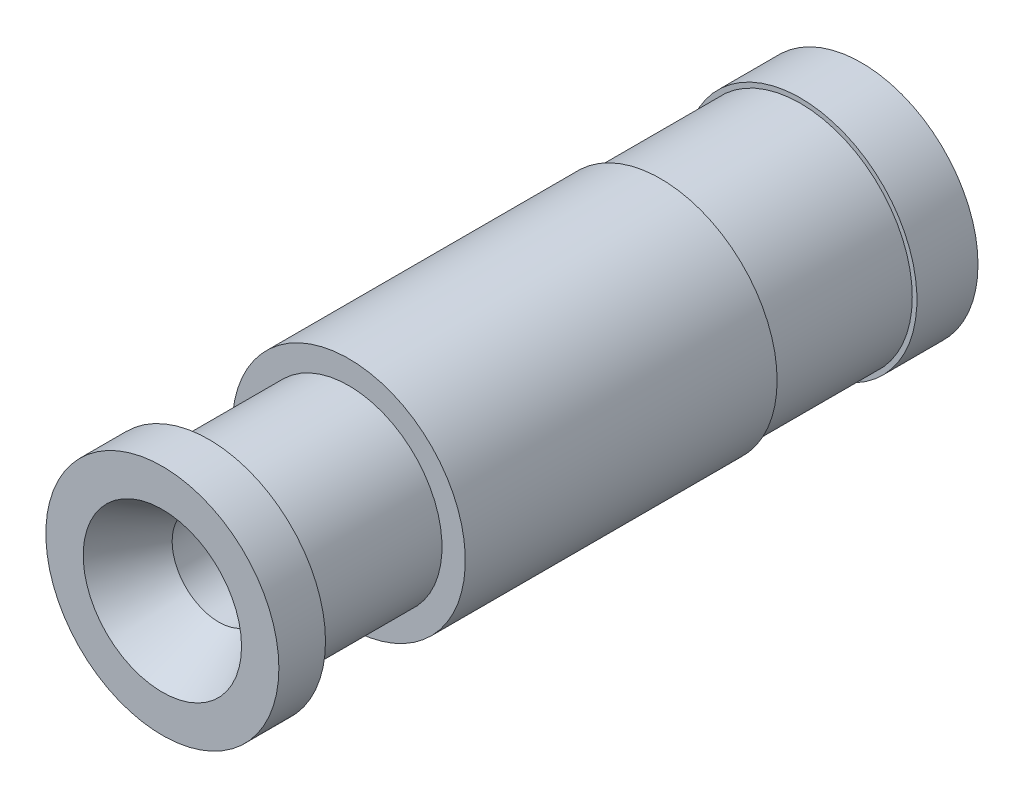
SolidWorks part; units mm, degrees
material "Brass"
ref_plane "Front Plane" through (0, 0, 0) normal (0, 0, 1) x (1, 0, 0)
ref_plane "Top Plane" through (0, 0, 0) normal (0, 1, 0) x (1, 0, 0)
ref_plane "Right Plane" through (0, 0, 0) normal (1, 0, 0) x (0, 0, -1)
sketch "Sketch1" plane through (0, 0, 0) normal (0, 0, 1) x (1, 0, 0)
  circle A0 centre (0, 0) radius 2.5
  dimension "D1" = 5
extrude "Boss-Extrude1" add sketch "Sketch1" along normal blind 15
sketch "Sketch2" plane through (0, 0, 0) normal (0, 0, -1) x (-1, 0, 0)
  circle A0 centre (0, 0) radius 1
  dimension "D1" = 2
extrude "Cut-Extrude1" cut sketch "Sketch2" against normal through all
hole_wizard "Tap Drill for M4x0.7 Tap1" positions "Sketch4" profile "Sketch3" hole size "M4x0.7" standard "ANSI Metric"
sketch "Sketch4" plane through (0, 0, 0) normal (0, 0, -1) x (-1, 0, 0)
  point P0 (0, 0)
cosmetic thread "Cosmetic Thread1" parameters "D1"=8, "D2"=4
sketch "Sketch3" plane through (0, 0, 0) normal (1, 0, 0) x (0, 1, 0)
  line L0 (0, 0) -> (0, 9.9914)
  line L1 (0, 9.9914) -> (1.65, 9)
  line L2 (1.65, 9) -> (1.65, 0)
  line L5 (1.65, 0) -> (0, 0)
  line L10 (0, 9.9914) -> (-1.65, 9) construction
  line L11 (0, -6.35) -> (0, 107.95) construction
  dimension "Hole Dia." = 3.3
  dimension "Hole Depth" = 9
  dimension "Drill Angle" = 118
sketch "Sketch5" plane through (0, 0, 0) normal (1, 0, 0) x (0, 0, -1)
  line L0 (0, 0) -> (-16.1108, 0) construction
  line L1 (-14, 3.7938) -> (-11, 3.7938)
  line L2 (-14, 3.7938) -> (-14, 2)
  line L3 (-14, 2) -> (-11, 2)
  line L4 (-11, 3.7938) -> (-11, 2)
  line L5 (-4.3101, 3.9267) -> (-4.3101, 2.4)
  line L6 (-4.3101, 2.4) -> (-1.3101, 2.4)
  line L7 (-1.3101, 2.4) -> (-1.3101, 3.9267)
  line L8 (-1.3101, 3.9267) -> (-4.3101, 3.9267)
  line L9 (0, 2.5) -> (-15, 2.5) construction
  dimension "D1" = 11
  dimension "D2" = 14
  dimension "D3" = 4
  dimension "D4" = 0.1
  dimension "D5" = 2
revolve "Cut-Revolve1" cut sketch "Sketch5" angle 360 mid plane about L0
chamfer "Chamfer1" distance 0.5 angle 60 1 edges at (-1.65, 0, 0)
chamfer "Chamfer2" distance 1.21 angle 30 1 edges at (-1, 0, 15)
